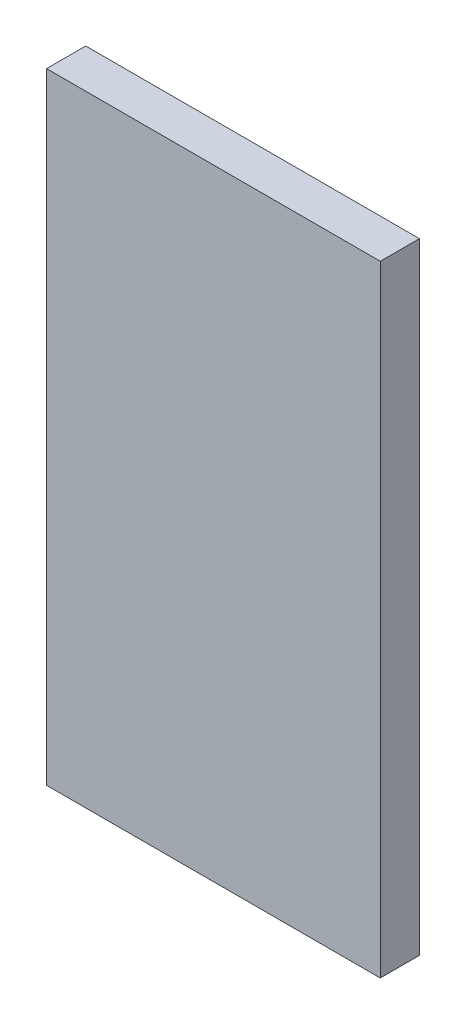
SolidWorks part; units mm, degrees
ref_plane "Front Plane" through (0, 0, 0) normal (0, 0, 1) x (1, 0, 0)
ref_plane "Top Plane" through (0, 0, 0) normal (0, 1, 0) x (1, 0, 0)
ref_plane "Right Plane" through (0, 0, 0) normal (1, 0, 0) x (0, 0, -1)
sketch "Sketch2" plane through (0, 0, 0) normal (0, 0, 1) x (1, 0, 0)
  line L0 (-42.6015, -332.9469) -> (-42.6015, -253.698)
  line L1 (-42.6015, -332.9469) -> (0, -332.9469)
  line L2 (-42.6015, -253.698) -> (0, -253.698)
  line L3 (0, -332.9469) -> (0, -253.698)
  line L4 (0, -267.4) -> (0, -226.9273) construction
  line L5 (7.8478, -332.9469) -> (-32.1522, -332.9469) construction
extrude "Boss-Extrude1" add sketch "Sketch2" against normal blind 5
